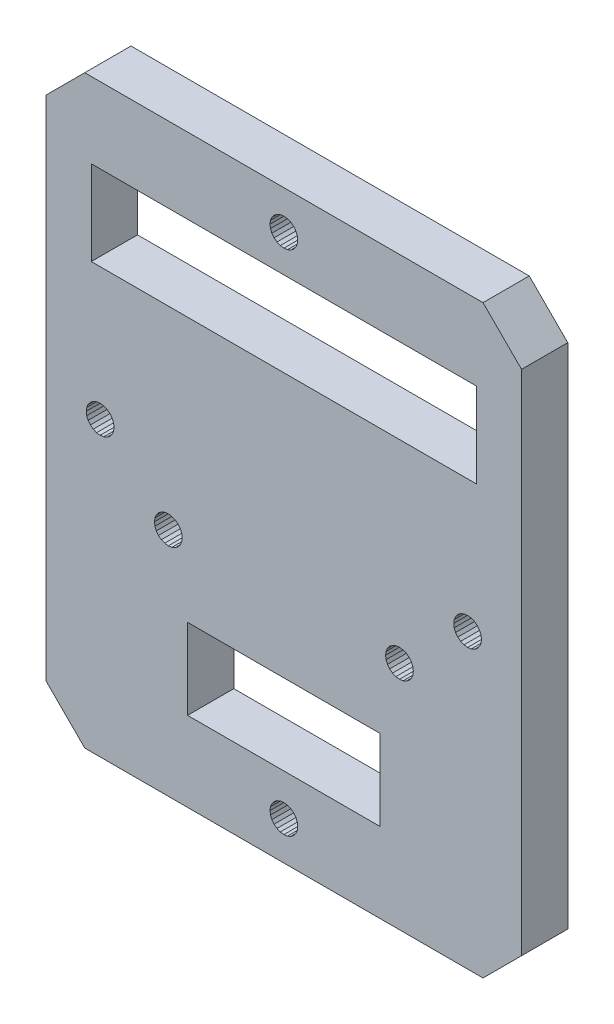
SolidWorks part; units mm, degrees
material "Maple"
ref_plane "Front Plane" through (0, 0, 0) normal (0, 0, 1) x (1, 0, 0)
ref_plane "Top Plane" through (0, 0, 0) normal (0, 1, 0) x (1, 0, 0)
ref_plane "Right Plane" through (0, 0, 0) normal (1, 0, 0) x (0, 0, -1)
sketch "Sketch1" plane through (0, 0, 0) normal (0, 0, 1) x (1, 0, 0)
  line L0 (-27.2158, 127.309) -> (-27.2158, 116.8518)
  line L1 (-27.2158, 116.8518) -> (-52.2158, 116.8518)
  line L2 (-65.562, 106.5018) -> (-13.8696, 106.5018)
  line L3 (-70.562, 111.5018) -> (-65.562, 106.5018)
  line L4 (-8.8696, 111.5018) -> (-8.8696, 177.4161)
  line L5 (-13.8696, 106.5018) -> (-8.8696, 111.5018)
  line L6 (-70.562, 177.4161) -> (-70.562, 111.5018)
  line L7 (-70.562, 177.4161) -> (-65.562, 182.4161)
  line L8 (-13.8696, 182.4161) -> (-65.562, 182.4161)
  line L9 (-13.8696, 182.4161) -> (-8.8696, 177.4161)
  line L10 (-52.2158, 116.8518) -> (-52.2158, 127.309)
  line L11 (-52.2158, 127.309) -> (-27.2158, 127.309)
  line L12 (-14.7158, 161.6089) -> (-64.7158, 161.6089)
  line L13 (-64.7158, 161.6089) -> (-64.7158, 172.6089)
  line L14 (-64.7158, 172.6089) -> (-14.7158, 172.6089)
  line L15 (-14.7158, 172.6089) -> (-14.7158, 161.6089)
  line L16 (-64.0279, 142.7203) -> (-63.562, 142.659)
  line L17 (-64.462, 142.9001) -> (-64.0279, 142.7203)
  line L18 (-64.8348, 145.7317) -> (-65.1209, 145.359)
  line L19 (-64.462, 146.0178) -> (-64.8348, 145.7317)
  line L20 (-64.0279, 146.1976) -> (-64.462, 146.0178)
  line L21 (-63.562, 146.259) -> (-64.0279, 146.1976)
  line L22 (-65.1209, 143.559) -> (-64.8348, 143.1862)
  line L23 (-65.3007, 143.9931) -> (-65.1209, 143.559)
  line L24 (-65.362, 144.459) -> (-65.3007, 143.9931)
  line L25 (-62.662, 146.0178) -> (-63.0961, 146.1976)
  line L26 (-62.2892, 143.1862) -> (-62.0032, 143.559)
  line L27 (-65.3007, 144.9248) -> (-65.362, 144.459)
  line L28 (-62.2892, 145.7317) -> (-62.662, 146.0178)
  line L29 (-62.0032, 145.359) -> (-62.2892, 145.7317)
  line L30 (-61.8234, 144.9248) -> (-62.0032, 145.359)
  line L31 (-61.762, 144.459) -> (-61.8234, 144.9248)
  line L32 (-61.8234, 143.9931) -> (-61.762, 144.459)
  line L33 (-62.0032, 143.559) -> (-61.8234, 143.9931)
  line L34 (-62.662, 142.9001) -> (-62.2892, 143.1862)
  line L35 (-63.0961, 142.7203) -> (-62.662, 142.9001)
  line L36 (-63.562, 142.659) -> (-63.0961, 142.7203)
  line L37 (-65.1209, 145.359) -> (-65.3007, 144.9248)
  line L38 (-64.8348, 143.1862) -> (-64.462, 142.9001)
  line L39 (-63.0961, 146.1976) -> (-63.562, 146.259)
  line L40 (-15.8696, 146.259) -> (-16.3355, 146.1976)
  line L41 (-17.6083, 144.9248) -> (-17.6696, 144.459)
  line L42 (-16.3355, 146.1976) -> (-16.7696, 146.0178)
  line L43 (-16.7696, 146.0178) -> (-17.1424, 145.7317)
  line L44 (-17.1424, 145.7317) -> (-17.4284, 145.359)
  line L45 (-17.4284, 145.359) -> (-17.6083, 144.9248)
  line L46 (-16.7696, 142.9001) -> (-16.3355, 142.7203)
  line L47 (-16.3355, 142.7203) -> (-15.8696, 142.659)
  line L48 (-17.1424, 143.1862) -> (-16.7696, 142.9001)
  line L49 (-14.9696, 146.0178) -> (-15.4037, 146.1976)
  line L50 (-14.5968, 143.1862) -> (-14.3107, 143.559)
  line L51 (-14.5968, 145.7317) -> (-14.9696, 146.0178)
  line L52 (-14.3107, 145.359) -> (-14.5968, 145.7317)
  line L53 (-14.1309, 144.9248) -> (-14.3107, 145.359)
  line L54 (-14.0696, 144.459) -> (-14.1309, 144.9248)
  line L55 (-14.1309, 143.9931) -> (-14.0696, 144.459)
  line L56 (-15.4037, 146.1976) -> (-15.8696, 146.259)
  line L57 (-14.3107, 143.559) -> (-14.1309, 143.9931)
  line L58 (-15.8696, 142.659) -> (-15.4037, 142.7203)
  line L59 (-15.4037, 142.7203) -> (-14.9696, 142.9001)
  line L60 (-14.9696, 142.9001) -> (-14.5968, 143.1862)
  line L61 (-17.6696, 144.459) -> (-17.6083, 143.9931)
  line L62 (-17.6083, 143.9931) -> (-17.4284, 143.559)
  line L63 (-17.4284, 143.559) -> (-17.1424, 143.1862)
  line L64 (-37.9771, 111.9677) -> (-38.157, 112.4018)
  line L65 (-37.9158, 111.5018) -> (-37.9771, 111.9677)
  line L66 (-37.9771, 111.036) -> (-37.9158, 111.5018)
  line L67 (-38.157, 110.6018) -> (-37.9771, 111.036)
  line L68 (-38.8158, 109.943) -> (-38.443, 110.229)
  line L69 (-39.2499, 109.7632) -> (-38.8158, 109.943)
  line L70 (-39.7158, 109.7018) -> (-39.2499, 109.7632)
  line L71 (-41.2747, 112.4018) -> (-41.4545, 111.9677)
  line L72 (-40.9886, 110.229) -> (-40.6158, 109.943)
  line L73 (-39.2499, 113.2405) -> (-39.7158, 113.3018)
  line L74 (-40.6158, 113.0607) -> (-40.9886, 112.7746)
  line L75 (-40.1817, 113.2405) -> (-40.6158, 113.0607)
  line L76 (-39.7158, 113.3018) -> (-40.1817, 113.2405)
  line L77 (-41.2747, 110.6018) -> (-40.9886, 110.229)
  line L78 (-41.4545, 111.036) -> (-41.2747, 110.6018)
  line L79 (-41.5158, 111.5018) -> (-41.4545, 111.036)
  line L80 (-38.8158, 113.0607) -> (-39.2499, 113.2405)
  line L81 (-38.443, 110.229) -> (-38.157, 110.6018)
  line L82 (-41.4545, 111.9677) -> (-41.5158, 111.5018)
  line L83 (-38.443, 112.7746) -> (-38.8158, 113.0607)
  line L84 (-38.157, 112.4018) -> (-38.443, 112.7746)
  line L85 (-40.9886, 112.7746) -> (-41.2747, 112.4018)
  line L86 (-40.1817, 109.7632) -> (-39.7158, 109.7018)
  line L87 (-40.6158, 109.943) -> (-40.1817, 109.7632)
  line L88 (-37.9771, 176.9502) -> (-37.9158, 177.4161)
  line L89 (-39.2499, 175.6774) -> (-38.8158, 175.8572)
  line L90 (-38.8158, 175.8572) -> (-38.443, 176.1433)
  line L91 (-38.443, 176.1433) -> (-38.157, 176.5161)
  line L92 (-38.157, 176.5161) -> (-37.9771, 176.9502)
  line L93 (-37.9771, 177.882) -> (-38.157, 178.3161)
  line L94 (-37.9158, 177.4161) -> (-37.9771, 177.882)
  line L95 (-41.2747, 178.3161) -> (-41.4545, 177.882)
  line L96 (-40.9886, 176.1433) -> (-40.6158, 175.8572)
  line L97 (-39.2499, 179.1547) -> (-39.7158, 179.2161)
  line L98 (-41.5158, 177.4161) -> (-41.4545, 176.9502)
  line L99 (-41.4545, 176.9502) -> (-41.2747, 176.5161)
  line L100 (-41.2747, 176.5161) -> (-40.9886, 176.1433)
  line L101 (-40.6158, 175.8572) -> (-40.1817, 175.6774)
  line L102 (-40.1817, 175.6774) -> (-39.7158, 175.6161)
  line L103 (-39.7158, 175.6161) -> (-39.2499, 175.6774)
  line L104 (-40.9886, 178.6889) -> (-41.2747, 178.3161)
  line L105 (-38.157, 178.3161) -> (-38.443, 178.6889)
  line L106 (-38.443, 178.6889) -> (-38.8158, 178.9749)
  line L107 (-38.8158, 178.9749) -> (-39.2499, 179.1547)
  line L108 (-40.6158, 178.9749) -> (-40.9886, 178.6889)
  line L109 (-40.1817, 179.1547) -> (-40.6158, 178.9749)
  line L110 (-39.7158, 179.2161) -> (-40.1817, 179.1547)
  line L111 (-41.4545, 177.882) -> (-41.5158, 177.4161)
  line L112 (-55.1817, 134.7203) -> (-54.7158, 134.659)
  line L113 (-55.6158, 134.9001) -> (-55.1817, 134.7203)
  line L114 (-55.9886, 135.1862) -> (-55.6158, 134.9001)
  line L115 (-23.157, 137.359) -> (-23.443, 137.7317)
  line L116 (-23.443, 135.1862) -> (-23.157, 135.559)
  line L117 (-23.443, 137.7317) -> (-23.8158, 138.0178)
  line L118 (-22.9771, 135.9931) -> (-22.9158, 136.459)
  line L119 (-22.9771, 136.9248) -> (-23.157, 137.359)
  line L120 (-24.7158, 134.659) -> (-24.2499, 134.7203)
  line L121 (-23.157, 135.559) -> (-22.9771, 135.9931)
  line L122 (-23.8158, 138.0178) -> (-24.2499, 138.1976)
  line L123 (-26.2747, 137.359) -> (-26.4545, 136.9248)
  line L124 (-25.6158, 138.0178) -> (-25.9886, 137.7317)
  line L125 (-24.7158, 138.259) -> (-25.1817, 138.1976)
  line L126 (-25.9886, 137.7317) -> (-26.2747, 137.359)
  line L127 (-25.1817, 138.1976) -> (-25.6158, 138.0178)
  line L128 (-54.2499, 138.1976) -> (-54.7158, 138.259)
  line L129 (-53.8158, 134.9001) -> (-53.443, 135.1862)
  line L130 (-54.2499, 134.7203) -> (-53.8158, 134.9001)
  line L131 (-54.7158, 134.659) -> (-54.2499, 134.7203)
  line L132 (-56.2747, 137.359) -> (-56.4545, 136.9248)
  line L133 (-55.9886, 137.7317) -> (-56.2747, 137.359)
  line L134 (-55.6158, 138.0178) -> (-55.9886, 137.7317)
  line L135 (-55.1817, 138.1976) -> (-55.6158, 138.0178)
  line L136 (-54.7158, 138.259) -> (-55.1817, 138.1976)
  line L137 (-56.2747, 135.559) -> (-55.9886, 135.1862)
  line L138 (-56.4545, 135.9931) -> (-56.2747, 135.559)
  line L139 (-56.5158, 136.459) -> (-56.4545, 135.9931)
  line L140 (-56.4545, 136.9248) -> (-56.5158, 136.459)
  line L141 (-53.443, 137.7317) -> (-53.8158, 138.0178)
  line L142 (-53.157, 137.359) -> (-53.443, 137.7317)
  line L143 (-52.9771, 136.9248) -> (-53.157, 137.359)
  line L144 (-52.9158, 136.459) -> (-52.9771, 136.9248)
  line L145 (-52.9771, 135.9931) -> (-52.9158, 136.459)
  line L146 (-53.157, 135.559) -> (-52.9771, 135.9931)
  line L147 (-53.8158, 138.0178) -> (-54.2499, 138.1976)
  line L148 (-25.9886, 135.1862) -> (-25.6158, 134.9001)
  line L149 (-26.2747, 135.559) -> (-25.9886, 135.1862)
  line L150 (-26.4545, 135.9931) -> (-26.2747, 135.559)
  line L151 (-26.5158, 136.459) -> (-26.4545, 135.9931)
  line L152 (-26.4545, 136.9248) -> (-26.5158, 136.459)
  line L153 (-24.2499, 138.1976) -> (-24.7158, 138.259)
  line L154 (-53.443, 135.1862) -> (-53.157, 135.559)
  line L155 (-22.9158, 136.459) -> (-22.9771, 136.9248)
  line L156 (-23.8158, 134.9001) -> (-23.443, 135.1862)
  line L157 (-24.2499, 134.7203) -> (-23.8158, 134.9001)
  line L158 (-25.1817, 134.7203) -> (-24.7158, 134.659)
  line L159 (-25.6158, 134.9001) -> (-25.1817, 134.7203)
  line L8460 (-42.0021, 139.8818) -> (-42.0021, 144.1897)
  line L8461 (-42.0021, 144.1897) -> (-39.8417, 139.8818)
  line L8462 (-39.8417, 139.8818) -> (-39.8417, 144.1897)
  line L8463 (-39.8417, 144.1897) -> (-39.8417, 139.8818)
  line L8464 (-39.8417, 139.8818) -> (-42.0021, 144.1897)
  line L8465 (-42.0021, 144.1897) -> (-42.0021, 139.8818)
  line L8466 (-37.9686, 144.1958) -> (-39.0051, 143.4779)
  line L8467 (-39.0051, 143.4779) -> (-37.9686, 144.1958)
  line L8468 (-37.9686, 144.1958) -> (-37.9686, 139.8818)
  line L8469 (-37.9686, 139.8818) -> (-37.9686, 144.1958)
extrude "Boss-Extrude1" add sketch "Sketch1" along normal blind 6
